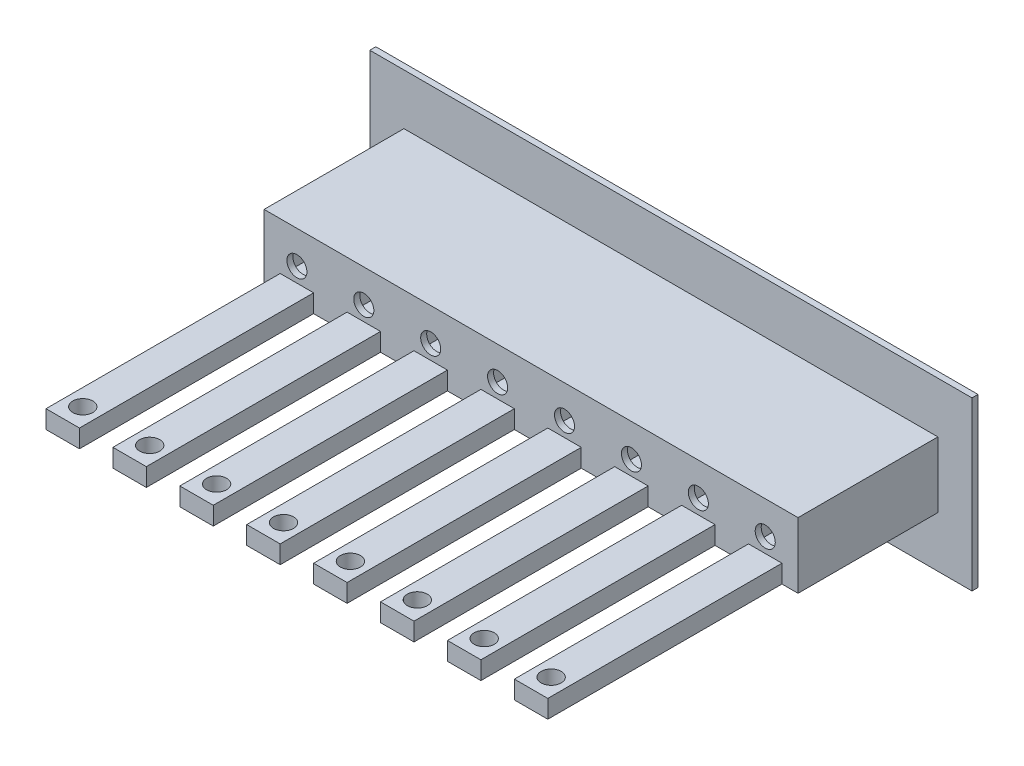
SolidWorks part; units mm, degrees
ref_plane "Alzado" through (0, 0, 0) normal (0, 0, 1) x (1, 0, 0)
ref_plane "Planta" through (0, 0, 0) normal (0, 1, 0) x (1, 0, 0)
ref_plane "Vista lateral" through (0, 0, 0) normal (1, 0, 0) x (0, 0, -1)
sketch "Croquis1" plane through (0, 0, 0) normal (0, 0, 1) x (1, 0, 0)
  line L1 (-92.4288, 22.3529) -> (-2.4288, 22.3529)
  line L2 (-92.4288, 22.3529) -> (-92.4288, -2.6471)
  line L3 (-92.4288, -2.6471) -> (-2.4288, -2.6471)
  line L4 (-2.4288, 22.3529) -> (-2.4288, -2.6471)
  dimension "D1" = 90
  dimension "D2" = 25
extrude "Saliente-Extruir1" add sketch "Croquis1" along normal blind 0.9
sketch "Croquis2" plane through (0, 0, 0.9) normal (0, 0, 1) x (1, 0, 0)
  line L0 (-2.4288, 22.3529) -> (-92.4288, 22.3529) construction
  line L1 (-86.4288, 13.8529) -> (-78.4288, 13.8529)
  line L2 (-86.4288, 13.8529) -> (-86.4288, 5.8529)
  line L3 (-86.4288, 5.8529) -> (-78.4288, 5.8529)
  line L4 (-78.4288, 13.8529) -> (-78.4288, 5.8529)
  line L6 (-92.4288, 22.3529) -> (-92.4288, -2.6471) construction
  line L7 (-76.4288, 13.8529) -> (-68.4288, 13.8529)
  line L8 (-76.4288, 13.8529) -> (-76.4288, 5.8529)
  line L9 (-76.4288, 5.8529) -> (-68.4288, 5.8529)
  line L10 (-68.4288, 13.8529) -> (-68.4288, 5.8529)
  line L11 (-66.4288, 13.8529) -> (-58.4288, 13.8529)
  line L12 (-66.4288, 13.8529) -> (-66.4288, 5.8529)
  line L13 (-66.4288, 5.8529) -> (-58.4288, 5.8529)
  line L14 (-58.4288, 13.8529) -> (-58.4288, 5.8529)
  line L15 (-56.4288, 13.8529) -> (-48.4288, 13.8529)
  line L16 (-56.4288, 13.8529) -> (-56.4288, 5.8529)
  line L17 (-56.4288, 5.8529) -> (-48.4288, 5.8529)
  line L18 (-48.4288, 13.8529) -> (-48.4288, 5.8529)
  line L19 (-46.4288, 13.8529) -> (-38.4288, 13.8529)
  line L20 (-46.4288, 13.8529) -> (-46.4288, 5.8529)
  line L21 (-46.4288, 5.8529) -> (-38.4288, 5.8529)
  line L22 (-38.4288, 13.8529) -> (-38.4288, 5.8529)
  line L23 (-36.4288, 13.8529) -> (-28.4288, 13.8529)
  line L24 (-36.4288, 13.8529) -> (-36.4288, 5.8529)
  line L25 (-36.4288, 5.8529) -> (-28.4288, 5.8529)
  line L26 (-28.4288, 13.8529) -> (-28.4288, 5.8529)
  line L27 (-26.4288, 13.8529) -> (-18.4288, 13.8529)
  line L28 (-26.4288, 13.8529) -> (-26.4288, 5.8529)
  line L29 (-26.4288, 5.8529) -> (-18.4288, 5.8529)
  line L30 (-18.4288, 13.8529) -> (-18.4288, 5.8529)
  line L31 (-16.4288, 13.8529) -> (-8.4288, 13.8529)
  line L32 (-16.4288, 13.8529) -> (-16.4288, 5.8529)
  line L33 (-16.4288, 5.8529) -> (-8.4288, 5.8529)
  line L34 (-8.4288, 13.8529) -> (-8.4288, 5.8529)
  dimension "D1" = 8
  dimension "D2" = 8
  dimension "D3" = 8.5
  dimension "D4" = 6
  dimension "D5" = 8
extrude "Cortar-Extruir1" cut sketch "Croquis2" against normal up to vertex (0.9 mm away)
sketch "Croquis3" plane through (0, 0, 0.9) normal (0, 0, 1) x (1, 0, 0)
  line L0 (-86.4288, 13.8529) -> (-86.4288, 5.8529) construction
  line L1 (-87.3288, 14.7529) -> (-7.5288, 14.7529)
  line L2 (-87.3288, 14.7529) -> (-87.3288, 4.9529)
  line L3 (-87.3288, 4.9529) -> (-7.5288, 4.9529)
  line L4 (-7.5288, 14.7529) -> (-7.5288, 4.9529)
  line L5 (-78.4288, 13.8529) -> (-86.4288, 13.8529) construction
  line L6 (-8.4288, 5.8529) -> (-8.4288, 13.8529) construction
  line L7 (-16.4288, 5.8529) -> (-8.4288, 5.8529) construction
  line L8 (-76.4288, 13.8529) -> (-68.4288, 13.8529)
  line L9 (-86.4288, 13.8529) -> (-78.4288, 13.8529)
  line L10 (-86.4288, 13.8529) -> (-86.4288, 5.8529)
  line L11 (-86.4288, 5.8529) -> (-78.4288, 5.8529)
  line L12 (-78.4288, 13.8529) -> (-78.4288, 5.8529)
  line L13 (-76.4288, 13.8529) -> (-76.4288, 5.8529)
  line L14 (-76.4288, 5.8529) -> (-68.4288, 5.8529)
  line L15 (-68.4288, 13.8529) -> (-68.4288, 5.8529)
  line L16 (-66.4288, 13.8529) -> (-58.4288, 13.8529)
  line L17 (-66.4288, 13.8529) -> (-66.4288, 5.8529)
  line L18 (-66.4288, 5.8529) -> (-58.4288, 5.8529)
  line L19 (-58.4288, 13.8529) -> (-58.4288, 5.8529)
  line L20 (-56.4288, 13.8529) -> (-48.4288, 13.8529)
  line L21 (-56.4288, 13.8529) -> (-56.4288, 5.8529)
  line L22 (-56.4288, 5.8529) -> (-48.4288, 5.8529)
  line L23 (-48.4288, 13.8529) -> (-48.4288, 5.8529)
  line L24 (-46.4288, 13.8529) -> (-38.4288, 13.8529)
  line L25 (-46.4288, 13.8529) -> (-46.4288, 5.8529)
  line L26 (-46.4288, 5.8529) -> (-38.4288, 5.8529)
  line L27 (-38.4288, 13.8529) -> (-38.4288, 5.8529)
  line L28 (-36.4288, 13.8529) -> (-28.4288, 13.8529)
  line L29 (-36.4288, 13.8529) -> (-36.4288, 5.8529)
  line L30 (-36.4288, 5.8529) -> (-28.4288, 5.8529)
  line L31 (-28.4288, 13.8529) -> (-28.4288, 5.8529)
  line L32 (-26.4288, 13.8529) -> (-18.4288, 13.8529)
  line L33 (-26.4288, 13.8529) -> (-26.4288, 5.8529)
  line L34 (-26.4288, 5.8529) -> (-18.4288, 5.8529)
  line L35 (-18.4288, 13.8529) -> (-18.4288, 5.8529)
  line L36 (-16.4288, 13.8529) -> (-8.4288, 13.8529)
  line L37 (-16.4288, 13.8529) -> (-16.4288, 5.8529)
  line L38 (-16.4288, 5.8529) -> (-8.4288, 5.8529)
  line L39 (-8.4288, 13.8529) -> (-8.4288, 5.8529)
  dimension "D1" = 0.9
  dimension "D2" = 0.9
  dimension "D3" = 0.9
  dimension "D4" = 0.9
  dimension "D5" = 8
extrude "Saliente-Extruir2" add sketch "Croquis3" along normal blind 20
sketch "Croquis4" plane through (0, 0, 20.9) normal (0, 0, 1) x (1, 0, 0)
  line L1 (-87.3288, 14.7529) -> (-7.5288, 14.7529)
  line L2 (-87.3288, 14.7529) -> (-87.3288, 4.9529)
  line L3 (-87.3288, 4.9529) -> (-7.5288, 4.9529)
  line L4 (-7.5288, 14.7529) -> (-7.5288, 4.9529)
  circle A0 centre (-82.4288, 9.8529) radius 1.5
  circle A1 centre (-72.4288, 9.8529) radius 1.5
  circle A2 centre (-62.4288, 9.8529) radius 1.5
  circle A3 centre (-52.4288, 9.8529) radius 1.5
  circle A4 centre (-42.4288, 9.8529) radius 1.5
  circle A5 centre (-32.4288, 9.8529) radius 1.5
  circle A6 centre (-22.4288, 9.8529) radius 1.5
  circle A7 centre (-12.4288, 9.8529) radius 1.5
  dimension "D1" = 8
extrude "Saliente-Extruir3" add sketch "Croquis4" along normal blind 0.9
sketch "Croquis5" plane through (0, 4.9529, 0) normal (0, -1, 0) x (1, 0, 0)
  line L0 (-87.3288, 21.8) -> (-84.9288, 21.8) construction
  line L1 (-87.3288, 21.8) -> (-7.5288, 21.8) construction
  line L2 (-84.9288, 21.8) -> (-79.9288, 21.8)
  line L3 (-79.9288, 21.8) -> (-79.9288, 56.8)
  line L4 (-79.9288, 56.8) -> (-84.9288, 56.8)
  line L5 (-84.9288, 56.8) -> (-84.9288, 21.8)
  line L6 (-74.9288, 21.8) -> (-69.9288, 21.8)
  line L7 (-69.9288, 21.8) -> (-69.9288, 56.8)
  line L8 (-69.9288, 56.8) -> (-74.9288, 56.8)
  line L9 (-74.9288, 56.8) -> (-74.9288, 21.8)
  line L10 (-77.3288, 21.8) -> (-74.9288, 21.8) construction
  line L11 (-64.9288, 21.8) -> (-59.9288, 21.8)
  line L12 (-59.9288, 21.8) -> (-59.9288, 56.8)
  line L13 (-59.9288, 56.8) -> (-64.9288, 56.8)
  line L14 (-64.9288, 56.8) -> (-64.9288, 21.8)
  line L15 (-67.3288, 21.8) -> (-64.9288, 21.8) construction
  line L16 (-54.9288, 21.8) -> (-49.9288, 21.8)
  line L17 (-49.9288, 21.8) -> (-49.9288, 56.8)
  line L18 (-49.9288, 56.8) -> (-54.9288, 56.8)
  line L19 (-54.9288, 56.8) -> (-54.9288, 21.8)
  line L20 (-57.3288, 21.8) -> (-54.9288, 21.8) construction
  line L21 (-44.9288, 21.8) -> (-39.9288, 21.8)
  line L22 (-39.9288, 21.8) -> (-39.9288, 56.8)
  line L23 (-39.9288, 56.8) -> (-44.9288, 56.8)
  line L24 (-44.9288, 56.8) -> (-44.9288, 21.8)
  line L25 (-47.3288, 21.8) -> (-44.9288, 21.8) construction
  line L26 (-34.9288, 21.8) -> (-29.9288, 21.8)
  line L27 (-29.9288, 21.8) -> (-29.9288, 56.8)
  line L28 (-29.9288, 56.8) -> (-34.9288, 56.8)
  line L29 (-34.9288, 56.8) -> (-34.9288, 21.8)
  line L30 (-37.3288, 21.8) -> (-34.9288, 21.8) construction
  line L31 (-24.9288, 21.8) -> (-19.9288, 21.8)
  line L32 (-19.9288, 21.8) -> (-19.9288, 56.8)
  line L33 (-19.9288, 56.8) -> (-24.9288, 56.8)
  line L34 (-24.9288, 56.8) -> (-24.9288, 21.8)
  line L35 (-27.3288, 21.8) -> (-24.9288, 21.8) construction
  line L36 (-14.9288, 21.8) -> (-9.9288, 21.8)
  line L37 (-9.9288, 21.8) -> (-9.9288, 56.8)
  line L38 (-9.9288, 56.8) -> (-14.9288, 56.8)
  line L39 (-14.9288, 56.8) -> (-14.9288, 21.8)
  line L40 (-17.3288, 21.8) -> (-14.9288, 21.8) construction
  circle A0 centre (-82.4288, 53.8) radius 1.5
  circle A1 centre (-72.4288, 53.8) radius 1.5
  circle A2 centre (-62.4288, 53.8) radius 1.5
  circle A3 centre (-52.4288, 53.8) radius 1.5
  circle A4 centre (-42.4288, 53.8) radius 1.5
  circle A5 centre (-32.4288, 53.8) radius 1.5
  circle A6 centre (-22.4288, 53.8) radius 1.5
  circle A7 centre (-12.4288, 53.8) radius 1.5
  dimension "D1" = 3
  dimension "D2" = 8
extrude "Saliente-Extruir4" add sketch "Croquis5" against normal blind 2.7
